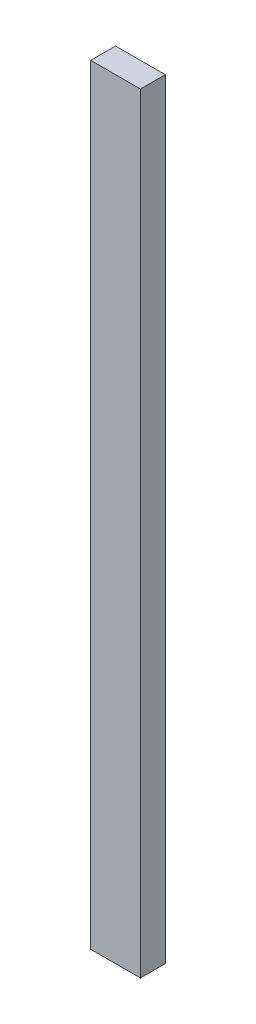
SolidWorks part; units mm, degrees
ref_plane "Front Plane" through (0, 0, 0) normal (0, 0, 1) x (1, 0, 0)
ref_plane "Top Plane" through (0, 0, 0) normal (0, 1, 0) x (1, 0, 0)
ref_plane "Right Plane" through (0, 0, 0) normal (1, 0, 0) x (0, 0, -1)
sketch "Sketch1" plane through (0, 0, 0) normal (0, 1, 0) x (1, 0, 0)
  line L1 (0, 0) -> (50.8, 0)
  line L2 (0, 0) -> (0, 25.4)
  line L3 (0, 25.4) -> (50.8, 25.4)
  line L4 (50.8, 0) -> (50.8, 25.4)
  dimension "D1" = 50.8
  dimension "D2" = 25.4
extrude "Boss-Extrude1" add sketch "Sketch1" along normal blind 787.4
